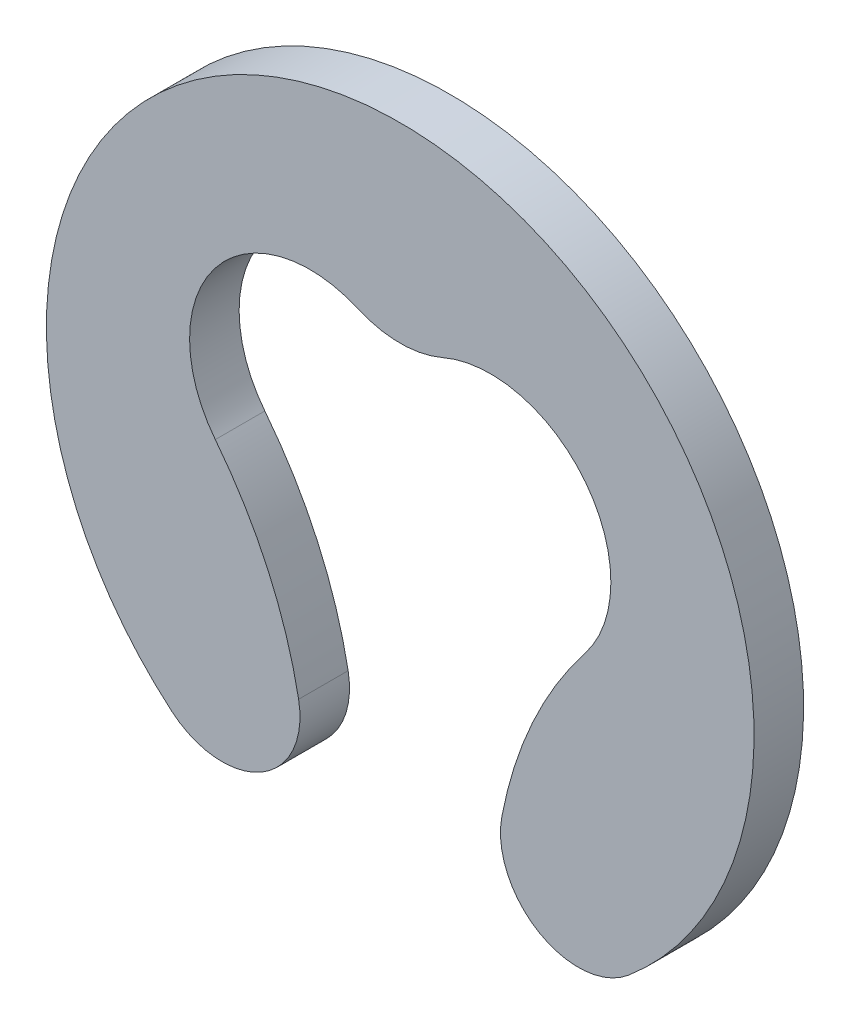
SolidWorks part; units mm, degrees
ref_plane "Alzado" through (0, 0, 0) normal (0, 0, 1) x (1, 0, 0)
ref_plane "Planta" through (0, 0, 0) normal (0, 1, 0) x (1, 0, 0)
ref_plane "Vista lateral" through (0, 0, 0) normal (1, 0, 0) x (0, 0, -1)
sketch "Croquis1" plane through (0, 0, 0) normal (0, 0, 1) x (1, 0, 0)
  circle A0 centre (0, 0) radius 5
  dimension "D1" = 10
extrude "Saliente-Extruir1" add sketch "Croquis1" along normal blind 0.7
sketch "Croquis2" plane through (0, 0, 0.7) normal (0, 0, 1) x (1, 0, 0)
  line L0 (0, 2.3) -> (0, -5) construction
  circle A0 centre (0, 0) radius 2.3 construction
  arc A1 (-0.5984, 2.4245) -> (0.5984, 2.4245) centre (0, 3.8) ccw
  arc A2 (-2.6133, -0.1847) -> (-1.4, -4.8) centre (-7.3309, -3.892) cw
  circle A3 centre (0, 0) radius 5 construction
  arc A4 (-0.5984, 2.4245) -> (-2.6133, -0.1847) centre (-1.2766, 0.8657) ccw
  arc A5 (2.6133, -0.1847) -> (1.4, -4.8) centre (7.3309, -3.892) ccw
  arc A6 (0.5984, 2.4245) -> (2.6133, -0.1847) centre (1.2766, 0.8657) cw
  arc A7 (-1.4, -4.8) -> (1.4, -4.8) centre (0, 0) ccw
  dimension "D1" = 4.6
  dimension "D3" = 1.7
  dimension "D4" = 6
  dimension "D2" = 3.8
  dimension "D5" = 1.4
extrude "Cortar-Extruir1" cut sketch "Croquis2" against normal up to next
fillet "Redondeo1" radius 1.1 2 edges at (1.4, -4.8, 0.35) (-1.4, -4.8, 0.35)
